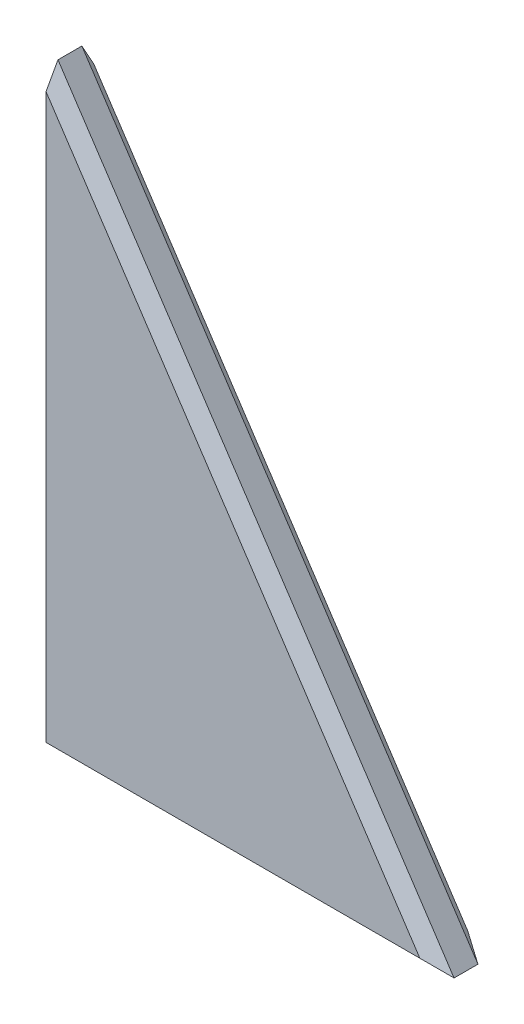
SolidWorks part; units mm, degrees
ref_plane "Front Plane" through (0, 0, 0) normal (0, 0, 1) x (1, 0, 0)
ref_plane "Top Plane" through (0, 0, 0) normal (0, 1, 0) x (1, 0, 0)
ref_plane "Right Plane" through (0, 0, 0) normal (1, 0, 0) x (0, 0, -1)
sketch "Sketch1" plane through (0, 0, 0) normal (0, 0, 1) x (1, 0, 0)
  line L0 (0, 63.5) -> (42.1211, 0)
  line L1 (0, 0) -> (42.1211, 0)
  line L2 (0, 0) -> (0, 63.5)
extrude "Extrude1" add sketch "Sketch1" along normal mid plane 5.08
chamfer "Chamfer1" distance 1.27 angle 45 4 edges at (21.0606, 31.75, -2.54) (21.0606, 31.75, 2.54) (21.0606, 0, -2.54) (21.0606, 0, 2.54)
